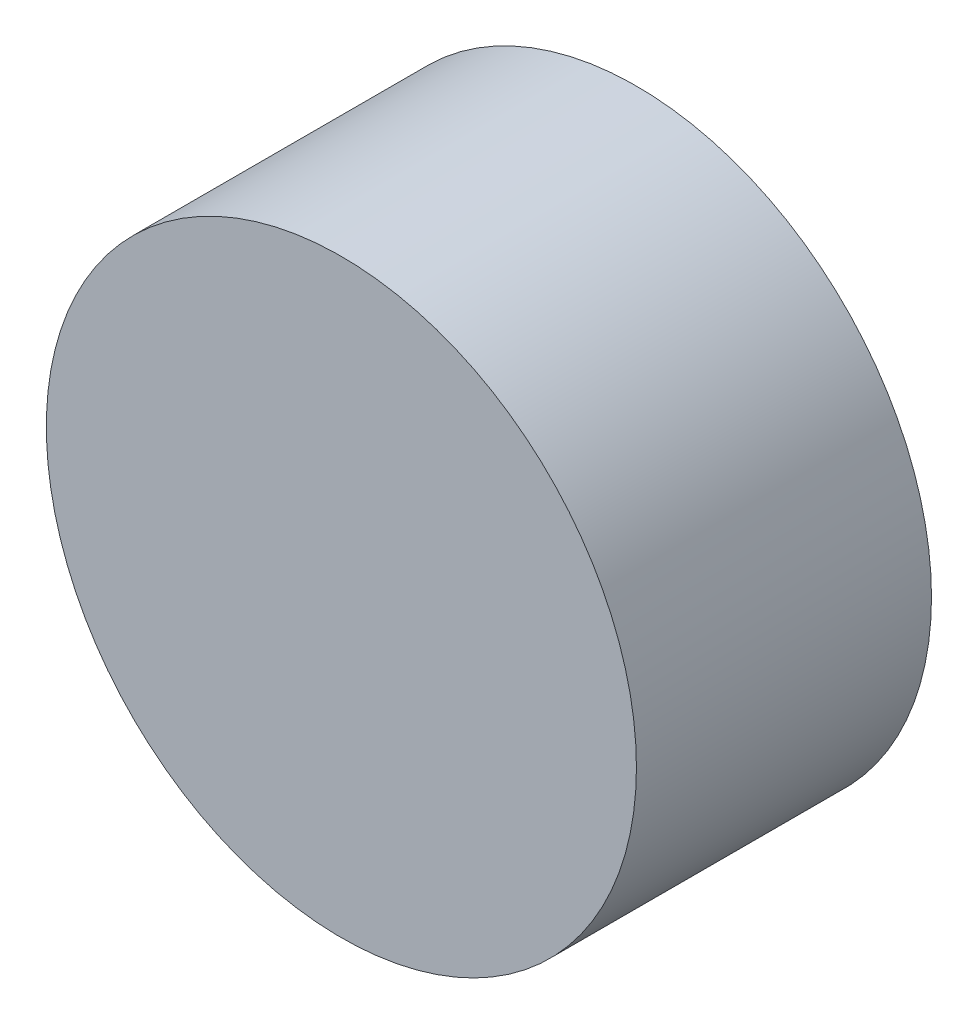
SolidWorks part; units mm, degrees
ref_plane "Front Plane" through (0, 0, 0) normal (0, 0, 1) x (1, 0, 0)
ref_plane "Top Plane" through (0, 0, 0) normal (0, 1, 0) x (1, 0, 0)
ref_plane "Right Plane" through (0, 0, 0) normal (1, 0, 0) x (0, 0, -1)
sketch "Sketch1" plane through (0, 0, 0) normal (0, 0, 1) x (1, 0, 0)
  circle A0 centre (0, 0) radius 3.175
  dimension "D1" = 6.35
extrude "Boss-Extrude1" add sketch "Sketch1" along normal blind 3.175
